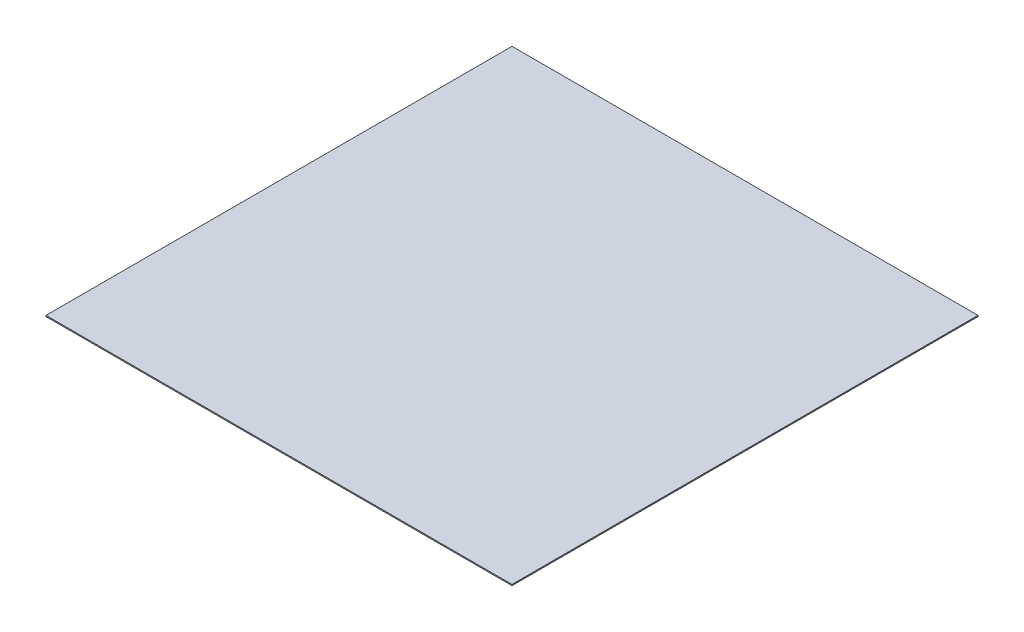
SolidWorks part; units mm, degrees
ref_plane "前视基准面" through (0, 0, 0) normal (0, 0, 1) x (1, 0, 0)
ref_plane "上视基准面" through (0, 0, 0) normal (0, 1, 0) x (1, 0, 0)
ref_plane "右视基准面" through (0, 0, 0) normal (1, 0, 0) x (0, 0, -1)
sketch "草图1" plane through (0, 0, 0) normal (0, 1, 0) x (1, 0, 0)
  line L1 (0, 0) -> (210, 0)
  line L2 (0, 0) -> (0, 210)
  line L3 (0, 210) -> (210, 210)
  line L4 (210, 0) -> (210, 210)
  dimension "D1" = 210
extrude "凸台-拉伸1" add sketch "草图1" along normal blind 0.5
